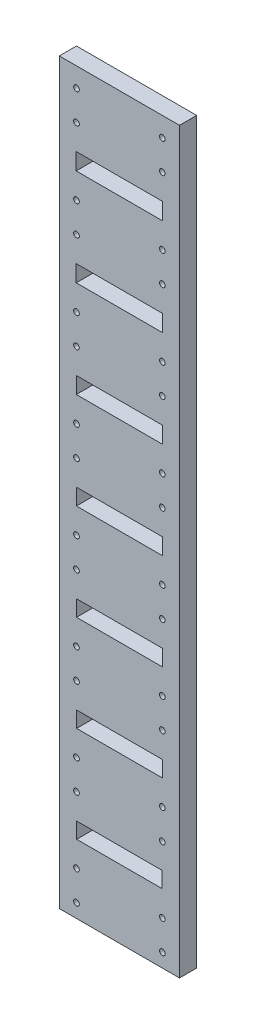
SolidWorks part; units mm, degrees
ref_plane "Front Plane" through (0, 0, 0) normal (0, 0, 1) x (1, 0, 0)
ref_plane "Top Plane" through (0, 0, 0) normal (0, 1, 0) x (1, 0, 0)
ref_plane "Right Plane" through (0, 0, 0) normal (1, 0, 0) x (0, 0, -1)
sketch "Sketch1" plane through (0, 0, 0) normal (0, 0, 1) x (1, 0, 0)
  line L0 (-25.2, 171.7) -> (25.2, 171.7)
  line L1 (-35, 215) -> (35, 215)
  line L2 (-35, 215) -> (-35, -215)
  line L3 (-35, -215) -> (35, -215)
  line L4 (35, 215) -> (35, -215)
  line L5 (-35, 215) -> (35, -215) construction
  line L6 (-35, -215) -> (35, 215) construction
  line L7 (24.9, -175) -> (-24.9, -175)
  line L8 (24.9, -175) -> (24.9, -165.8)
  line L9 (24.9, -165.8) -> (-24.9, -165.8)
  line L10 (-24.9, -175) -> (-24.9, -165.8)
  line L11 (24.9, -175) -> (-24.9, -165.8) construction
  line L12 (24.9, -165.8) -> (-24.9, -175) construction
  line L13 (24.95, -119.1) -> (-24.95, -119.1)
  line L14 (24.95, -119.1) -> (24.95, -109.8)
  line L15 (24.95, -109.8) -> (-24.95, -109.8)
  line L16 (-24.95, -119.1) -> (-24.95, -109.8)
  line L17 (24.95, -119.1) -> (-24.95, -109.8) construction
  line L18 (24.95, -109.8) -> (-24.95, -119.1) construction
  line L19 (25, -63.1) -> (-25, -63.1)
  line L20 (25, -63.1) -> (25, -53.7)
  line L21 (25, -53.7) -> (-25, -53.7)
  line L22 (-25, -63.1) -> (-25, -53.7)
  line L23 (25, -63.1) -> (-25, -53.7) construction
  line L24 (25, -53.7) -> (-25, -63.1) construction
  line L25 (25.05, -7) -> (-25.05, -7)
  line L26 (25.05, -7) -> (25.05, 2.5)
  line L27 (25.05, 2.5) -> (-25.05, 2.5)
  line L28 (-25.05, -7) -> (-25.05, 2.5)
  line L29 (25.05, -7) -> (-25.05, 2.5) construction
  line L30 (25.05, 2.5) -> (-25.05, -7) construction
  line L31 (25.1, 49.2) -> (-25.1, 49.2)
  line L32 (25.1, 49.2) -> (25.1, 58.8)
  line L33 (25.1, 58.8) -> (-25.1, 58.8)
  line L34 (-25.1, 49.2) -> (-25.1, 58.8)
  line L35 (25.1, 49.2) -> (-25.1, 58.8) construction
  line L36 (25.1, 58.8) -> (-25.1, 49.2) construction
  line L41 (-25.15, 115.2) -> (25.15, 115.2)
  line L42 (-25.15, 115.2) -> (-25.15, 105.5)
  line L43 (-25.15, 105.5) -> (25.15, 105.5)
  line L44 (25.15, 115.2) -> (25.15, 105.5)
  line L45 (-25.15, 115.2) -> (25.15, 105.5) construction
  line L46 (-25.15, 105.5) -> (25.15, 115.2) construction
  line L47 (-25.2, 171.7) -> (-25.2, 161.9)
  line L48 (-25.2, 161.9) -> (25.2, 161.9)
  line L49 (25.2, 171.7) -> (25.2, 161.9)
  line L50 (-25.2, 171.7) -> (25.2, 161.9) construction
  line L51 (-25.2, 161.9) -> (25.2, 171.7) construction
  point P0 (0, 0)
  point P6 (0, -170.4)
  point P11 (0, -114.45)
  point P16 (0, -58.4)
  point P21 (0, -2.25)
  point P26 (0, 54)
  point P31 (0, 110.35)
  point P37 (0, -215)
  point P38 (0, 166.8)
  dimension "D1" = 70
  dimension "D2" = 430
  dimension "D3" = 40
  dimension "D4" = 46.7
  dimension "D5" = 46.7
  dimension "D6" = 46.7
  dimension "D7" = 46.7
  dimension "D9" = 49.8
  dimension "D10" = 9.2
  dimension "D11" = 49.9
  dimension "D12" = 9.3
  dimension "D13" = 50
  dimension "D14" = 9.4
  dimension "D15" = 50.1
  dimension "D16" = 9.5
  dimension "D17" = 50.2
  dimension "D18" = 9.6
  dimension "D8" = 50.3
  dimension "D19" = 9.7
  dimension "D20" = 46.7
  dimension "D21" = 9.8
  dimension "D22" = 50.4
  dimension "D23" = 46.7
extrude "Boss-Extrude1" add sketch "Sketch1" along normal blind 10
hole_wizard "M4 Tapped Hole1" positions "Sketch2" profile "Sketch3" tap size "M4" standard "ISO" end condition through all
sketch "Sketch2" plane through (0, 0, 10) normal (0, 0, 1) x (1, 0, 0)
  line L1 (0, -215) -> (0, 215) construction
  line L2 (-35, -215) -> (35, -215) construction
  line L3 (35, 215) -> (-35, 215) construction
  line L5 (-24.9, -175) -> (24.9, -175) construction
  line L6 (-24.9, -170.4) -> (24.9, -170.4) construction
  line L7 (-24.9, -165.8) -> (-24.9, -175) construction
  line L8 (24.9, -175) -> (24.9, -165.8) construction
  line L11 (-24.95, -114.45) -> (24.95, -114.45) construction
  line L12 (-24.95, -109.8) -> (-24.95, -119.1) construction
  line L13 (24.95, -119.1) -> (24.95, -109.8) construction
  line L16 (-25, -58.4) -> (25, -58.4) construction
  line L17 (-25, -53.7) -> (-25, -63.1) construction
  line L18 (25, -63.1) -> (25, -53.7) construction
  line L20 (-25.05, -2.25) -> (25.05, -2.25) construction
  line L21 (-25.05, 2.5) -> (-25.05, -7) construction
  line L22 (25.05, -7) -> (25.05, 2.5) construction
  line L24 (-25.1, 54) -> (25.1, 54) construction
  line L25 (-25.1, 58.8) -> (-25.1, 49.2) construction
  line L26 (25.1, 49.2) -> (25.1, 58.8) construction
  line L28 (-25.15, 110.35) -> (25.15, 110.35) construction
  line L29 (-25.15, 115.2) -> (-25.15, 105.5) construction
  line L30 (25.15, 105.5) -> (25.15, 115.2) construction
  line L32 (-25.2, 166.8) -> (25.2, 166.8) construction
  line L33 (-25.2, 171.7) -> (-25.2, 161.9) construction
  line L34 (25.2, 161.9) -> (25.2, 171.7) construction
  point P0 (-25, -189.7)
  point P10 (25, -189.7)
  point P11 (25, -207)
  point P12 (-25, -207)
  point P38 (-25, -133.8)
  point P39 (25, -133.8)
  point P40 (25, -151.1)
  point P41 (-25, -151.1)
  point P90 (-25, -77.8)
  point P91 (25, -77.8)
  point P92 (25, -95.1)
  point P93 (-25, -95.1)
  point P94 (-25, -21.7)
  point P95 (25, -21.7)
  point P96 (25, -39)
  point P97 (-25, -39)
  point P98 (-25, 34.5)
  point P99 (25, 34.5)
  point P100 (25, 17.2)
  point P101 (-25, 17.2)
  point P102 (-25, 90.8)
  point P103 (25, 90.8)
  point P104 (25, 73.5)
  point P105 (-25, 73.5)
  point P106 (-25, 147.2)
  point P107 (25, 147.2)
  point P108 (25, 129.9)
  point P109 (-25, 129.9)
  point P110 (-25, 203.7)
  point P111 (25, 203.7)
  point P112 (25, 186.4)
  point P113 (-25, 186.4)
  dimension "D3" = 14.7
  dimension "D1" = 2
  dimension "D2" = 2
sketch "Sketch3" plane through (-25, -189.7, 10) normal (1, 0, 0) x (0, -1, 0)
  line L0 (0, 0) -> (0, 10)
  line L1 (0, 10) -> (1.65, 10)
  line L2 (1.65, 10) -> (1.65, 0)
  line L5 (1.65, 0) -> (0, 0)
  line L11 (0, -6.35) -> (0, 107.95) construction
  dimension "Thru Tap Drill Dia." = 3.3
  dimension "Thru Tap Drill Depth" = 10
cosmetic thread "Hole Thread1" parameters "D2"=4
cosmetic thread "Hole Thread2" parameters "D2"=4
cosmetic thread "Hole Thread3" parameters "D2"=4
cosmetic thread "Hole Thread4" parameters "D2"=4
cosmetic thread "Hole Thread5" parameters "D2"=4
cosmetic thread "Hole Thread6" parameters "D2"=4
cosmetic thread "Hole Thread7" parameters "D2"=4
cosmetic thread "Hole Thread8" parameters "D2"=4
cosmetic thread "Hole Thread9" parameters "D2"=4
cosmetic thread "Hole Thread10" parameters "D2"=4
cosmetic thread "Hole Thread11" parameters "D2"=4
cosmetic thread "Hole Thread12" parameters "D2"=4
cosmetic thread "Hole Thread13" parameters "D2"=4
cosmetic thread "Hole Thread14" parameters "D2"=4
cosmetic thread "Hole Thread15" parameters "D2"=4
cosmetic thread "Hole Thread16" parameters "D2"=4
cosmetic thread "Hole Thread17" parameters "D2"=4
cosmetic thread "Hole Thread18" parameters "D2"=4
cosmetic thread "Hole Thread19" parameters "D2"=4
cosmetic thread "Hole Thread20" parameters "D2"=4
cosmetic thread "Hole Thread21" parameters "D2"=4
cosmetic thread "Hole Thread22" parameters "D2"=4
cosmetic thread "Hole Thread23" parameters "D2"=4
cosmetic thread "Hole Thread24" parameters "D2"=4
cosmetic thread "Hole Thread25" parameters "D2"=4
cosmetic thread "Hole Thread26" parameters "D2"=4
cosmetic thread "Hole Thread27" parameters "D2"=4
cosmetic thread "Hole Thread28" parameters "D2"=4
cosmetic thread "Hole Thread29" parameters "D2"=4
cosmetic thread "Hole Thread30" parameters "D2"=4
cosmetic thread "Hole Thread31" parameters "D2"=4
cosmetic thread "Hole Thread32" parameters "D2"=4
equation "\"spacing\"= 46.7"
equation "\"D4@Sketch1\"=\"spacing\""
equation "\"D5@Sketch1\"=\"spacing\""
equation "\"D6@Sketch1\"=\"spacing\""
equation "\"D7@Sketch1\"=\"spacing\""
equation "\"D20@Sketch1\"=\"spacing\""
equation "\"D23@Sketch1\"=\"spacing\""
